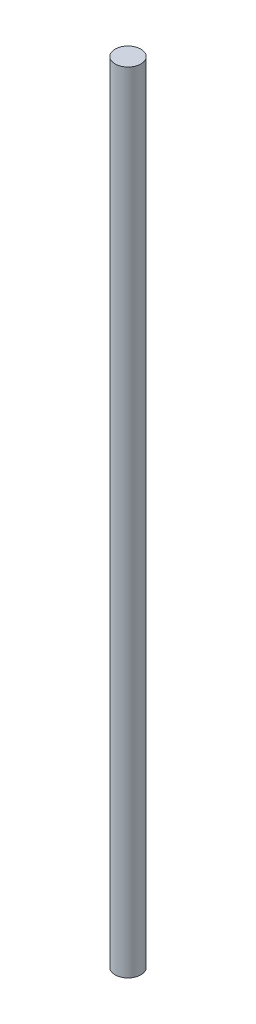
SolidWorks part; units mm, degrees
ref_plane "前视基准面" through (0, 0, 0) normal (0, 0, 1) x (1, 0, 0)
ref_plane "上视基准面" through (0, 0, 0) normal (0, 1, 0) x (1, 0, 0)
ref_plane "右视基准面" through (0, 0, 0) normal (1, 0, 0) x (0, 0, -1)
ref_plane "基准面4" through (0, 0, 0) normal (0, 0, -1) x (-1, 0, 0)
sketch "草图1" plane through (0, 0, 0) normal (0, 0, -1) x (-1, 0, 0)
  line L0 (-164, -245) -> (-160, -245)
  line L1 (-160, -245) -> (-160, 0)
  line L2 (-160, 0) -> (-164, 0)
  line L3 (-164, 0) -> (-164, -245)
  line L4 (-160, -245) -> (-160, 0) construction
revolve "旋转1" add sketch "草图1" angle 360 about L4
